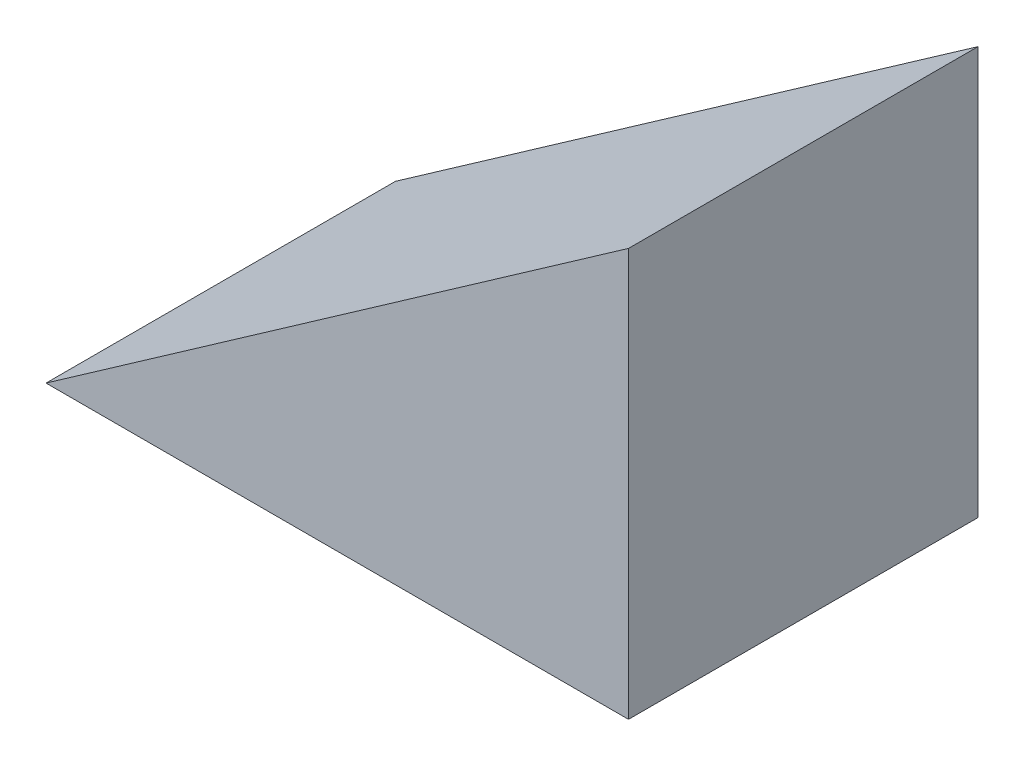
SolidWorks part; units mm, degrees
ref_plane "Front Plane" through (0, 0, 0) normal (0, 0, 1) x (1, 0, 0)
ref_plane "Top Plane" through (0, 0, 0) normal (0, 1, 0) x (1, 0, 0)
ref_plane "Right Plane" through (0, 0, 0) normal (1, 0, 0) x (0, 0, -1)
sketch "Sketch1" plane through (0, 0, 0) normal (0, 0, 1) x (1, 0, 0)
  line L0 (0, 0) -> (-50, 0)
  line L1 (-50, 0) -> (0, 35.0104)
  line L2 (0, 35.0104) -> (0, 0)
  dimension "D1" = 35
  dimension "D2" = 50
extrude "Boss-Extrude1" add sketch "Sketch1" along normal blind 30
